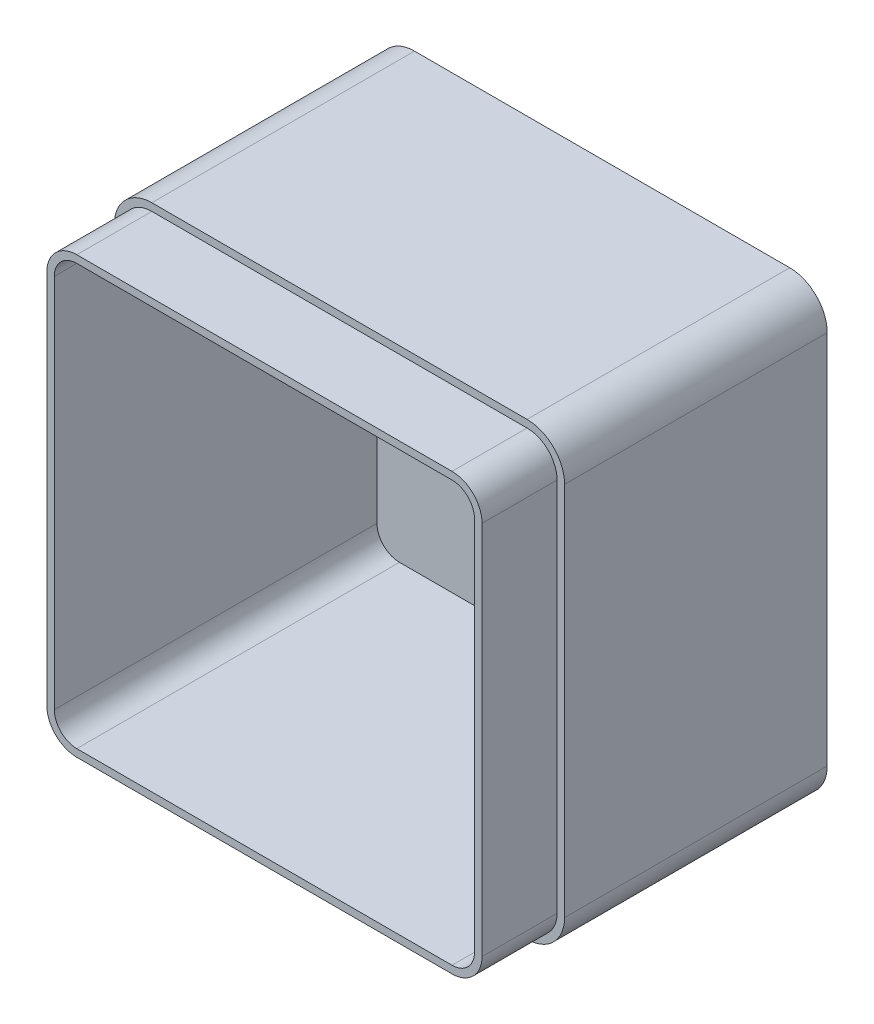
SolidWorks part; units mm, degrees
ref_plane "Front" through (0, 0, 0) normal (0, 0, 1) x (1, 0, 0)
ref_plane "Top" through (0, 0, 0) normal (0, 1, 0) x (1, 0, 0)
ref_plane "Right" through (0, 0, 0) normal (1, 0, 0) x (0, 0, -1)
sketch "Sketch1" plane through (0, 0, 0) normal (0, 0, 1) x (1, 0, 0)
  line L1 (0, 0) -> (120, 0)
  line L2 (0, 0) -> (0, 120)
  line L3 (0, 120) -> (120, 120)
  line L4 (120, 0) -> (120, 120)
  dimension "D1" = 120
  dimension "D2" = 120
extrude "Boss-Extrude1" add sketch "Sketch1" along normal blind 90
fillet "Fillet1" radius 10 4 edges at (0, 0, 45) (120, 0, 45) (120, 120, 45) (0, 120, 45)
shell "Shell1" thickness 4
sketch "Sketch2" plane through (0, 0, 90) normal (0, 0, 1) x (1, 0, 0)
  line L4 (0, 110) -> (0, 10)
  line L5 (10, 0) -> (110, 0)
  line L6 (120, 10) -> (120, 110)
  line L7 (110, 120) -> (10, 120)
  line L8 (0, 110) -> (0, 10)
  line L9 (10, 0) -> (110, 0)
  line L10 (120, 10) -> (120, 110)
  line L11 (110, 120) -> (10, 120)
  line L16 (2, 110) -> (2, 10)
  line L17 (10, 2) -> (110, 2)
  line L18 (118, 10) -> (118, 110)
  line L19 (110, 118) -> (10, 118)
  line L20 (2, 110) -> (2, 10)
  line L21 (10, 2) -> (110, 2)
  line L22 (118, 10) -> (118, 110)
  line L23 (110, 118) -> (10, 118)
  arc A4 (0, 10) -> (10, 0) centre (10, 10) ccw
  arc A5 (110, 0) -> (120, 10) centre (110, 10) ccw
  arc A6 (120, 110) -> (110, 120) centre (110, 110) ccw
  arc A7 (10, 120) -> (0, 110) centre (10, 110) ccw
  arc A8 (0, 10) -> (10, 0) centre (10, 10) ccw
  arc A9 (110, 0) -> (120, 10) centre (110, 10) ccw
  arc A10 (120, 110) -> (110, 120) centre (110, 110) ccw
  arc A11 (10, 120) -> (0, 110) centre (10, 110) ccw
  arc A16 (2, 10) -> (10, 2) centre (10, 10) ccw
  arc A17 (110, 2) -> (118, 10) centre (110, 10) ccw
  arc A18 (118, 110) -> (110, 118) centre (110, 110) ccw
  arc A19 (10, 118) -> (2, 110) centre (10, 110) ccw
  arc A20 (2, 10) -> (10, 2) centre (10, 10) ccw
  arc A21 (110, 2) -> (118, 10) centre (110, 10) ccw
  arc A22 (118, 110) -> (110, 118) centre (110, 110) ccw
  arc A23 (10, 118) -> (2, 110) centre (10, 110) ccw
  dimension "D1" = 0
  dimension "D2" = 2
extrude "Cut-Extrude1" cut sketch "Sketch2" against normal blind 20
